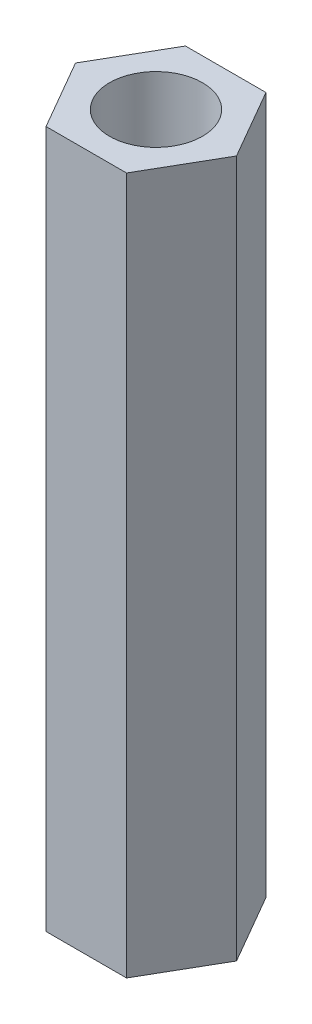
SolidWorks part; units mm, degrees
ref_plane "前视基准面" through (0, 0, 0) normal (0, 0, 1) x (1, 0, 0)
ref_plane "上视基准面" through (0, 0, 0) normal (0, 1, 0) x (1, 0, 0)
ref_plane "右视基准面" through (0, 0, 0) normal (1, 0, 0) x (0, 0, -1)
sketch "草图1" plane through (0, 0, 0) normal (0, 1, 0) x (1, 0, 0)
  line L0 (-1.7321, 3) -> (1.7321, 3)
  line L1 (1.7321, 3) -> (3.4641, 0)
  line L2 (3.4641, 0) -> (1.7321, -3)
  line L3 (1.7321, -3) -> (-1.7321, -3)
  line L4 (-1.7321, -3) -> (-3.4641, 0)
  line L5 (-3.4641, 0) -> (-1.7321, 3)
  line L6 (-3.4641, 0) -> (3.4641, 0) construction
  line L7 (0, 3) -> (0, -3) construction
  point P8 (0, 0)
  dimension "D1" = 6
  dimension "D2" = 6
  dimension "D3" = 6
  dimension "D4" = 120
  dimension "D5" = 120
extrude "凸台-拉伸1" add sketch "草图1" along normal blind 30
sketch "草图2" plane through (0, 30, 0) normal (0, 1, 0) x (1, 0, 0)
  circle A0 centre (0, 0) radius 2
  dimension "D1" = 4
extrude "切除-拉伸1" cut sketch "草图2" against normal up to next and the other way through all
